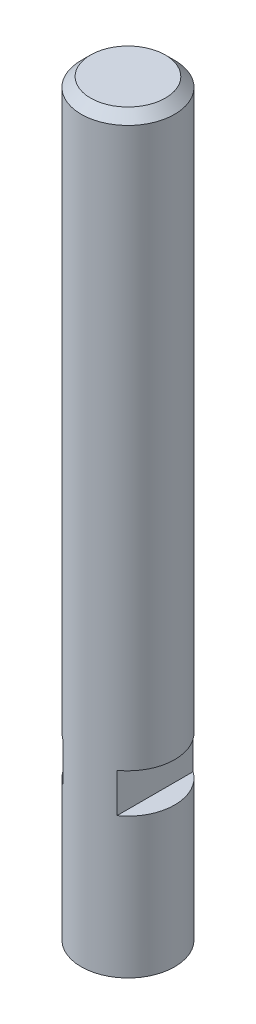
SolidWorks part; units mm, degrees
material "1.4301 (X5CrNi18-10)"
ref_plane "Vorne" through (0, 0, 0) normal (0, 0, 1) x (1, 0, 0)
ref_plane "Oben" through (0, 0, 0) normal (0, 1, 0) x (1, 0, 0)
ref_plane "Rechts" through (0, 0, 0) normal (1, 0, 0) x (0, 0, -1)
sketch "Skizze1" plane through (0, 0, 0) normal (1, 0, 0) x (0, 0, -1)
  line L0 (0, 0) -> (0, -50.5828) construction
  line L1 (0, 80) -> (-5, 80)
  line L2 (-5, 80) -> (-5, 0)
  line L5 (-5, 0) -> (0, 0)
  line L6 (0, 0) -> (0, 80)
  dimension "D1" = 80
  dimension "D3" = 10
revolve "Rotation1" add sketch "Skizze1" angle 360 about L0
hole_wizard "M4 Gewindebohrung1" positions "Skizze4" profile "Skizze3" tap size "M4" standard "DIN"
sketch "Skizze4" plane through (0, 0, 0) normal (0, -1, 0) x (-1, 0, 0)
  point P0 (0, 0)
sketch "Skizze3" plane through (0, 0, 0) normal (1, 0, 0) x (0, 0, -1)
  line L0 (0, 0) -> (0, 40.9914)
  line L1 (0, 40.9914) -> (1.65, 40)
  line L2 (1.65, 40) -> (1.65, 0)
  line L5 (1.65, 0) -> (0, 0)
  line L10 (0, 40.9914) -> (-1.65, 40) construction
  line L11 (0, -6.35) -> (0, 107.95) construction
  dimension "Bohrerdurchmesser" = 3.3
  dimension "Bohrungstiefe" = 40
  dimension "Spitzenwinkel" = 118
cosmetic thread "Bohrungsgewinde1" parameters "D1"=50, "D2"=4
sketch "Skizze5" plane through (0, 0, 0) normal (0, 0, 1) x (1, 0, 0)
  line L0 (0, 0) -> (0, 15.7167) construction
  line L1 (-5, 80) -> (-5, 0) construction
  line L2 (-7.1, 19.2) -> (-2.9, 19.2)
  line L3 (-7.1, 19.2) -> (-7.1, 15)
  line L4 (-7.1, 15) -> (-2.9, 15)
  line L5 (-2.9, 19.2) -> (-2.9, 15)
  line L6 (-7.1, 19.2) -> (-2.9, 15) construction
  line L7 (-7.1, 15) -> (-2.9, 19.2) construction
  line L9 (-5, 0) -> (5, 0) construction
  point P3 (-5, 17.1)
  dimension "D1" = 15
  dimension "D2" = 5.8
  dimension "D3" = 4.2
extrude "Schnitt-Linear austragen1" cut sketch "Skizze5" against normal mid plane 20
mirror "Spiegeln1" about plane through (0, 0, 0) normal (1, 0, 0) of "Schnitt-Linear austragen1"
chamfer "Fase1" distance 1 angle 45 1 edges at (0, 80, 5)
